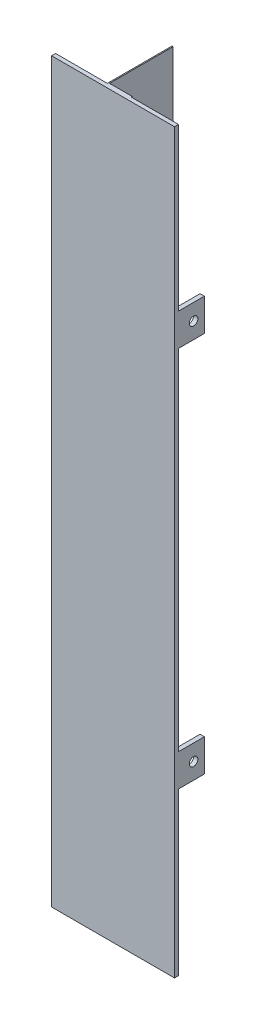
SolidWorks part; units mm, degrees
material "PPS"
ref_plane "Płaszczyzna XY" through (0, 0, 0) normal (0, 0, 1) x (1, 0, 0)
ref_plane "Płaszczyzna XZ" through (0, 0, 0) normal (0, 1, 0) x (1, 0, 0)
ref_plane "Płaszczyzna YZ" through (0, 0, 0) normal (1, 0, 0) x (0, 0, -1)
sketch "Szkic1" plane through (0, 0, 0) normal (0, 1, 0) x (1, 0, 0)
  line L0 (0, 0) -> (0, 1.85)
  line L1 (0, 1.85) -> (24, 1.85)
  line L2 (24, 1.85) -> (24, 31.85)
  line L3 (24, 31.85) -> (24.5, 31.85)
  line L4 (24.5, 31.85) -> (24.5, 2.35)
  line L5 (24.5, 2.35) -> (35, 2.35)
  line L6 (35, 2.35) -> (35, 1.85)
  line L7 (35, 1.85) -> (57, 1.85)
  line L8 (57, 1.85) -> (57, 0)
  line L9 (57, 0) -> (0, 0)
  dimension "D1" = 1.85
  dimension "D2" = 0.5
  dimension "D3" = 1.85
  dimension "D4" = 57
  dimension "D5" = 0.5
  dimension "D6" = 22
  dimension "D7" = 24
  dimension "D8" = 30
extrude "Dodanie-wyciągnięcie1" add sketch "Szkic1" along normal blind 342
sketch "Szkic3" plane through (0, 0, -1.85) normal (0, 0, -1) x (-1, 0, 0)
  line L0 (-57, 342) -> (-57, 0) construction
  line L1 (-57, 75) -> (-55, 75)
  line L2 (-57, 75) -> (-57, 90)
  line L3 (-57, 90) -> (-55, 90)
  line L4 (-55, 75) -> (-55, 90)
  line L5 (0, 342) -> (0, 0) construction
  line L10 (-57, 252) -> (-55, 252)
  line L11 (-57, 252) -> (-57, 267)
  line L12 (-57, 267) -> (-55, 267)
  line L13 (-55, 252) -> (-55, 267)
  line L14 (0, 75) -> (-2, 75)
  line L15 (0, 75) -> (0, 90)
  line L16 (0, 90) -> (-2, 90)
  line L17 (-2, 75) -> (-2, 90)
  line L18 (-24, 0) -> (0, 0) construction
  line L23 (0, 252) -> (-2, 252)
  line L24 (0, 252) -> (0, 267)
  line L25 (0, 267) -> (-2, 267)
  line L26 (-2, 252) -> (-2, 267)
  line L27 (-57, 0) -> (-35, 0) construction
  line L28 (-57, 342) -> (-35, 342) construction
  line L29 (-24, 342) -> (0, 342) construction
  dimension "D1" = 15
  dimension "D3" = 15
  dimension "D4" = 15
  dimension "D6" = 15
  dimension "D7" = 2
  dimension "D9" = 2
  dimension "D10" = 2
  dimension "D12" = 2
  dimension "D13" = 75
  dimension "D14" = 75
  dimension "D15" = 75
  dimension "D16" = 75
extrude "Dodanie-wyciągnięcie2" add sketch "Szkic3" along normal blind 12
sketch "Szkic4" plane through (0, 0, 0) normal (-1, 0, 0) x (0, 0, 1)
  line L0 (-13.85, 90) -> (-1.85, 90) construction
  line L1 (-13.85, 75) -> (-13.85, 90) construction
  line L2 (-13.85, 252) -> (-13.85, 267) construction
  line L3 (-13.85, 267) -> (-1.85, 267) construction
  circle A0 centre (-8.85, 82.5) radius 2
  circle A1 centre (-8.85, 259.5) radius 2
  dimension "D1" = 4
  dimension "D2" = 7.5
  dimension "D3" = 5
  dimension "D4" = 5
  dimension "D5" = 7.5
  dimension "D6" = 4
sketch "Szkic5" plane through (57, 0, 0) normal (1, 0, 0) x (0, 0, -1)
  circle A0 centre (8.85, 259.5) radius 2
  circle A1 centre (8.85, 82.5) radius 2
  dimension "D1" = 4
  dimension "D2" = 4
extrude "Wytnij-wyciągnięcie1" cut sketch "Szkic4" against normal blind 10
extrude "Wytnij-wyciągnięcie2" cut sketch "Szkic5" against normal blind 10
